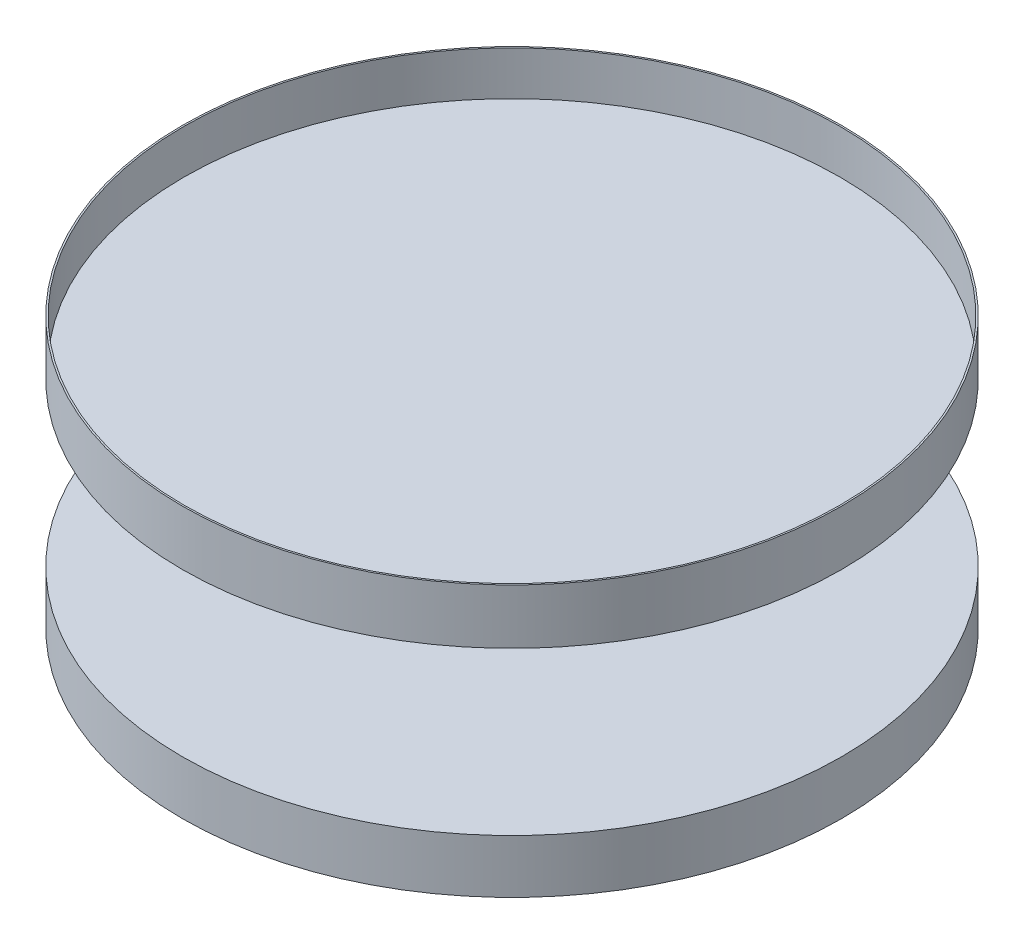
SolidWorks part; units mm, degrees
ref_plane "Front Plane" through (0, 0, 0) normal (0, 0, 1) x (1, 0, 0)
ref_plane "Top Plane" through (0, 0, 0) normal (0, 1, 0) x (1, 0, 0)
ref_plane "Right Plane" through (0, 0, 0) normal (1, 0, 0) x (0, 0, -1)
sketch "Sketch2" plane through (0, 0, 0) normal (0, 0, 1) x (1, 0, 0)
  line L0 (0, -99.6198) -> (645.625, -99.6198)
  line L1 (645.625, -99.6198) -> (645.625, 5.3802)
  line L2 (645.625, 5.3802) -> (16.1406, 5.3802)
  line L3 (16.1406, 5.3802) -> (16.1406, 322.8125)
  line L4 (16.1406, 322.8125) -> (645.625, 322.8125)
  line L5 (645.625, 322.8125) -> (645.625, 430.4166)
  line L6 (645.625, 430.4166) -> (642.3968, 430.4166)
  line L7 (642.3968, 430.4166) -> (642.3968, 344.3333)
  line L8 (642.3968, 344.3333) -> (0, 344.3333)
  line L9 (0, -99.6198) -> (0, 344.3333)
  dimension "D1" = 105
revolve "Revolve2" add sketch "Sketch2" angle 360 about L9
sketch "Sketch3" plane through (0, 430.4166, 0) normal (0, 1, 0) x (1, 0, 0)
  line L0 (642.3968, 0) -> (-642.3968, 0) construction
  circle A0 centre (0, 0) radius 642.3968 construction
sketch "Sketch4" plane through (0, 344.3333, 0) normal (0, 1, 0) x (1, 0, 0)
  circle A0 centre (0, 0) radius 245
